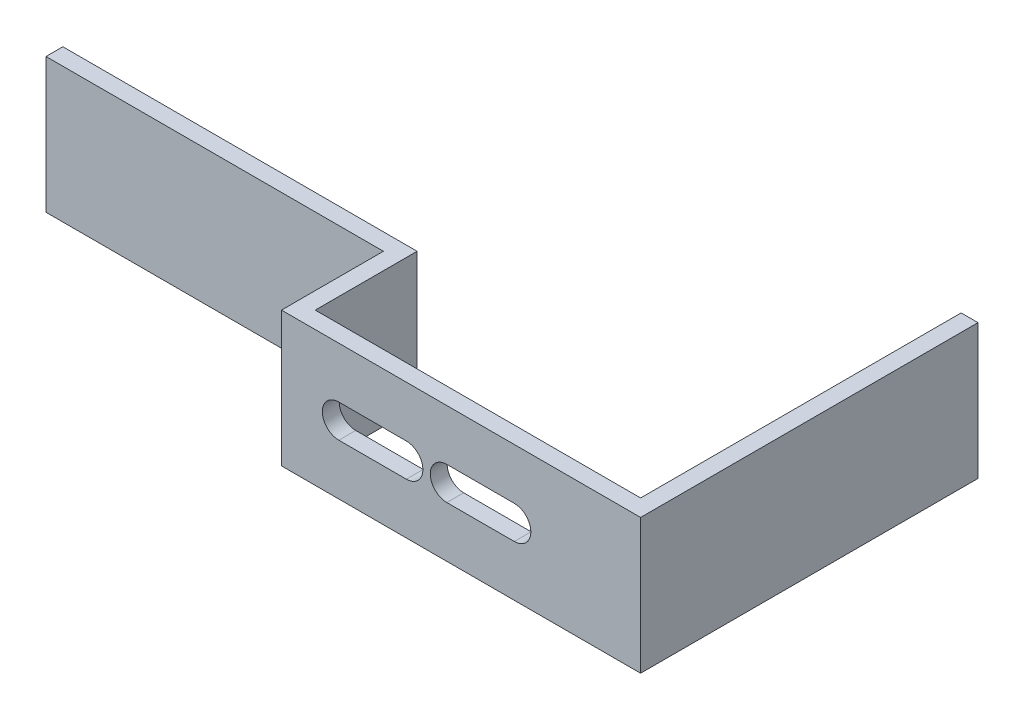
SolidWorks part; units mm, degrees
ref_plane "Front Plane" through (0, 0, 0) normal (0, 0, 1) x (1, 0, 0)
ref_plane "Top Plane" through (0, 0, 0) normal (0, 1, 0) x (1, 0, 0)
ref_plane "Right Plane" through (0, 0, 0) normal (1, 0, 0) x (0, 0, -1)
sketch "Sketch1" plane through (0, 0, 0) normal (0, 1, 0) x (1, 0, 0)
  line L1 (0, 0) -> (33.7947, 0)
  line L2 (0, 0) -> (0, 1.5875)
  line L3 (1.5875, 1.5875) -> (32.2072, 1.5875)
  line L4 (33.7947, 0) -> (33.7947, 1.5875)
  line L6 (0, 1.5875) -> (0, 9.5885)
  line L7 (0, 11.176) -> (1.5875, 11.176)
  line L8 (1.5875, 1.5875) -> (1.5875, 11.176)
  line L9 (0, 11.176) -> (-31.75, 11.176)
  line L11 (0, 9.5885) -> (-31.75, 9.5885)
  line L12 (-31.75, 11.176) -> (-31.75, 9.5885)
  line L14 (33.7947, 1.5875) -> (33.7947, 31.75)
  line L15 (33.7947, 31.75) -> (32.2072, 31.75)
  line L16 (32.2072, 1.5875) -> (32.2072, 31.75)
  dimension "D1" = 1.5875
  dimension "D2" = 30.6197
  dimension "D3" = 1.5875
  dimension "D4" = 31.75
  dimension "D5" = 9.5885
  dimension "D6" = 1.5875
  dimension "D7" = 1.5875
  dimension "D8" = 31.75
extrude "Boss-Extrude1" add sketch "Sketch1" along normal blind 12.7
sketch "Sketch2" plane through (0, 0, 0) normal (0, 0, 1) x (1, 0, 0)
  line L0 (5.3975, 6.35) -> (11.7475, 6.35) construction
  line L1 (5.3975, 7.9057) -> (11.7475, 7.9058)
  line L2 (5.3975, 4.7942) -> (11.7475, 4.7943)
  line L3 (0, 12.7) -> (0, 0) construction
  line L4 (13.6525, 12.7) -> (13.6525, 0) construction
  line L7 (21.9075, 6.35) -> (15.5575, 6.35) construction
  line L8 (21.9075, 7.9057) -> (15.5575, 7.9057)
  line L9 (21.9075, 4.7943) -> (15.5575, 4.7943)
  line L10 (8.5725, 6.35) -> (18.7325, 6.35) construction
  line L11 (0, 12.7) -> (33.7947, 12.7) construction
  line L12 (0, 0) -> (33.7947, 0) construction
  arc A0 (5.3975, 7.9057) -> (5.3975, 4.7942) centre (5.3975, 6.35) ccw
  arc A1 (11.7475, 4.7943) -> (11.7475, 7.9058) centre (11.7475, 6.35) ccw
  arc A2 (21.9075, 7.9057) -> (21.9075, 4.7943) centre (21.9075, 6.35) cw
  arc A3 (15.5575, 4.7943) -> (15.5575, 7.9057) centre (15.5575, 6.35) cw
  point P2 (8.5725, 6.35)
  point P9 (0, 6.35)
  point P18 (18.7325, 6.35)
  point P25 (13.6525, 6.35)
  dimension "D1" = 1.5557
  dimension "D2" = 6.35
  dimension "D3" = 10.16
  dimension "D4" = 13.6525
extrude "Cut-Extrude1" cut sketch "Sketch2" against normal through all
